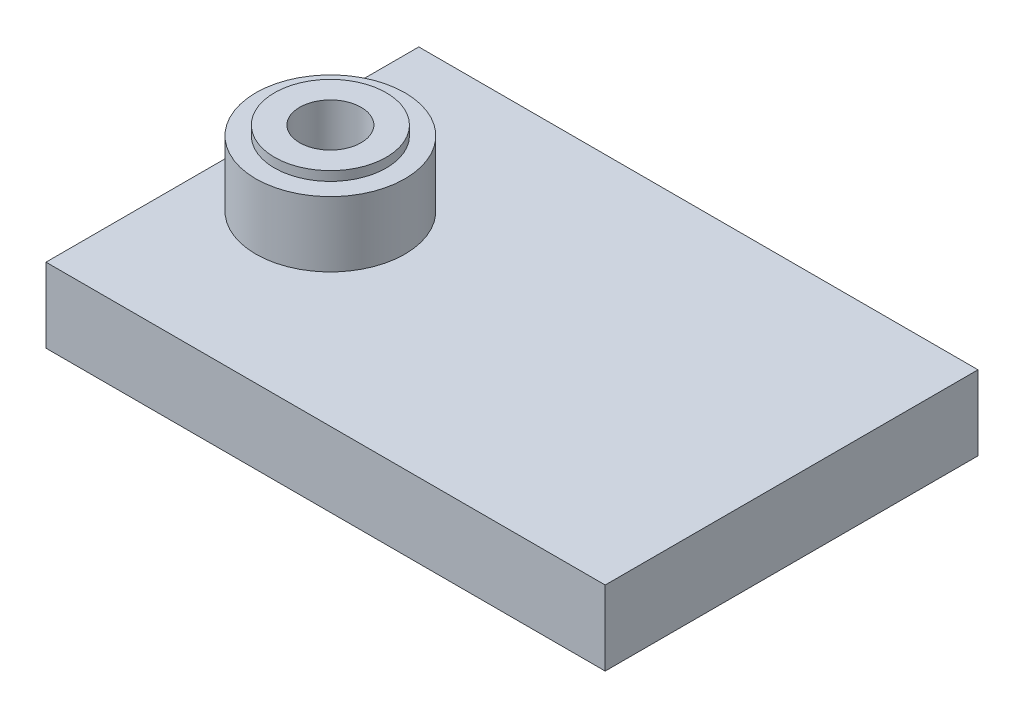
SolidWorks part; units mm, degrees
ref_plane "Front Plane" through (0, 0, 0) normal (0, 0, 1) x (1, 0, 0)
ref_plane "Top Plane" through (0, 0, 0) normal (0, 1, 0) x (1, 0, 0)
ref_plane "Right Plane" through (0, 0, 0) normal (1, 0, 0) x (0, 0, -1)
sketch "Sketch1" plane through (0, 0, 0) normal (0, 1, 0) x (1, 0, 0)
  line L0 (-5.2568, 10) -> (-5.2568, -10)
  line L1 (24.7432, 10) -> (-5.2568, 10)
  line L2 (24.7432, 10) -> (24.7432, -10)
  line L3 (24.7432, -10) -> (-5.2568, -10)
  line L5 (0, -10) -> (0, 10) construction
  line L6 (24.7432, 0) -> (-5.2568, 0) construction
  point P0 (0, 0)
  point P1 (15.308, 0)
  point P7 (0, 10)
  point P8 (0, -10)
  dimension "D1" = 30
  dimension "D2" = 5.2568
  dimension "D3" = 20
extrude "Boss-Extrude1" add sketch "Sketch1" along normal blind 4
sketch "Sketch2" plane through (0, 4, 0) normal (0, 1, 0) x (1, 0, 0)
  circle A0 centre (0, 0) radius 4
  dimension "D1" = 8
extrude "Boss-Extrude2" add sketch "Sketch2" along normal blind 3.5
hole_wizard "M4x0.7 Tapped Hole1" positions "Sketch3" profile "Sketch4" tap size "M4x0.7" standard "ANSI Metric" end condition through all
sketch "Sketch3" plane through (0, 0, 0) normal (0, -1, 0) x (-1, 0, 0)
  point P0 (0, 0)
sketch "Sketch4" plane through (0, 0, 0) normal (1, 0, 0) x (0, 0, -1)
  line L0 (0, 0) -> (0, 7.5)
  line L1 (0, 7.5) -> (1.65, 7.5)
  line L2 (1.65, 7.5) -> (1.65, 0)
  line L5 (1.65, 0) -> (0, 0)
  line L11 (0, -6.35) -> (0, 107.95) construction
  dimension "Thru Tap Drill Dia." = 3.3
  dimension "Thru Tap Drill Depth" = 7.5
cosmetic thread "Hole Thread1" parameters "D2"=4
sketch "Sketch6" plane through (0, 7.5, 0) normal (0, 1, 0) x (1, 0, 0)
  circle A0 centre (0, 0) radius 3
  circle A1 centre (0, 0) radius 1.65
  circle A2 centre (0, 0) radius 1.65
  dimension "D2" = 6
  dimension "D1" = 0
extrude "Boss-Extrude3" add sketch "Sketch6" along normal blind 0.5
